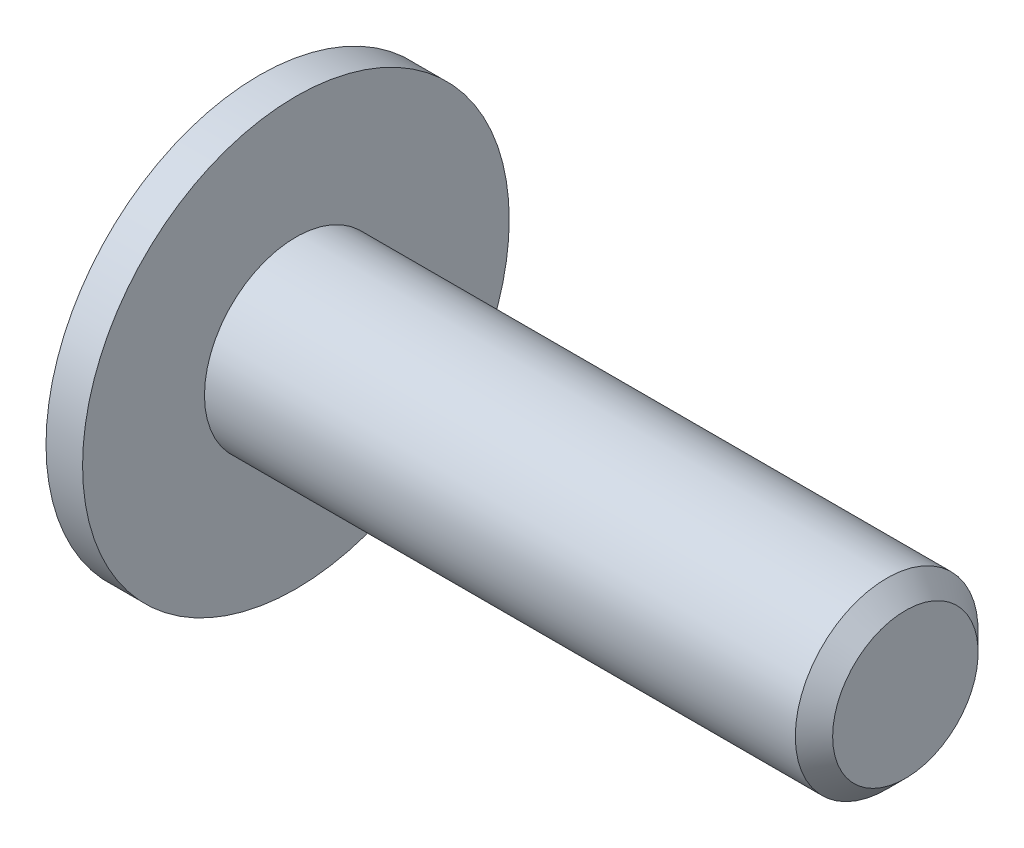
SolidWorks part; units mm, degrees
material "AISI 304"
ref_plane "正面" through (0, 0, 0) normal (0, 0, 1) x (1, 0, 0)
ref_plane "平面" through (0, 0, 0) normal (0, 1, 0) x (1, 0, 0)
ref_plane "右側面" through (0, 0, 0) normal (1, 0, 0) x (0, 0, -1)
ref_plane "Plane1" through (0, 0, 0) normal (0, 0, 1) x (1, 0, 0)
sketch "Sketch1" plane through (0, 0, 0) normal (0, 0, 1) x (1, 0, 0)
  line L0 (-1.65, 0) -> (-1.65, 1.95)
  line L1 (-0.6, 2.6) -> (-0.6, 3.5)
  line L2 (-0.6, 3.5) -> (0, 3.5)
  line L3 (0, 3.5) -> (0, 1.5)
  line L4 (0, 1.5) -> (9.6935, 1.5)
  line L5 (9.6935, 1.5) -> (10, 1.1935)
  line L6 (10, 1.1935) -> (10, 0)
  line L7 (10, 0) -> (-1.65, 0)
  line L8 (10, 0) -> (-1.65, 0) construction
  arc A0 (-1.65, 1.95) -> (-0.6, 2.6) centre (-0.2725, 0.8979) cw
  dimension "D1" = 1.5
revolve "Revolve1" add sketch "Sketch1" angle 360 about L8
cosmetic thread "Cosmetic Thread1" parameters "D1"=8.4691, "D2"=2.387
ref_plane "Plane2" through (-1.65, 0, 0) normal (1, 0, 0) x (0, 0, -1)
sketch "Sketch2" plane through (-1.65, 0, 0) normal (1, 0, 0) x (0, 0, -1)
  line L0 (-1, -0.5774) -> (0, -1.1547)
  line L1 (0, -1.1547) -> (1, -0.5774)
  line L2 (1, -0.5774) -> (1, 0.5774)
  line L3 (1, 0.5774) -> (0, 1.1547)
  line L4 (0, 1.1547) -> (-1, 0.5774)
  line L5 (-1, 0.5774) -> (-1, -0.5774)
extrude "Cut-Extrude1" cut sketch "Sketch2" along normal blind 1.05
